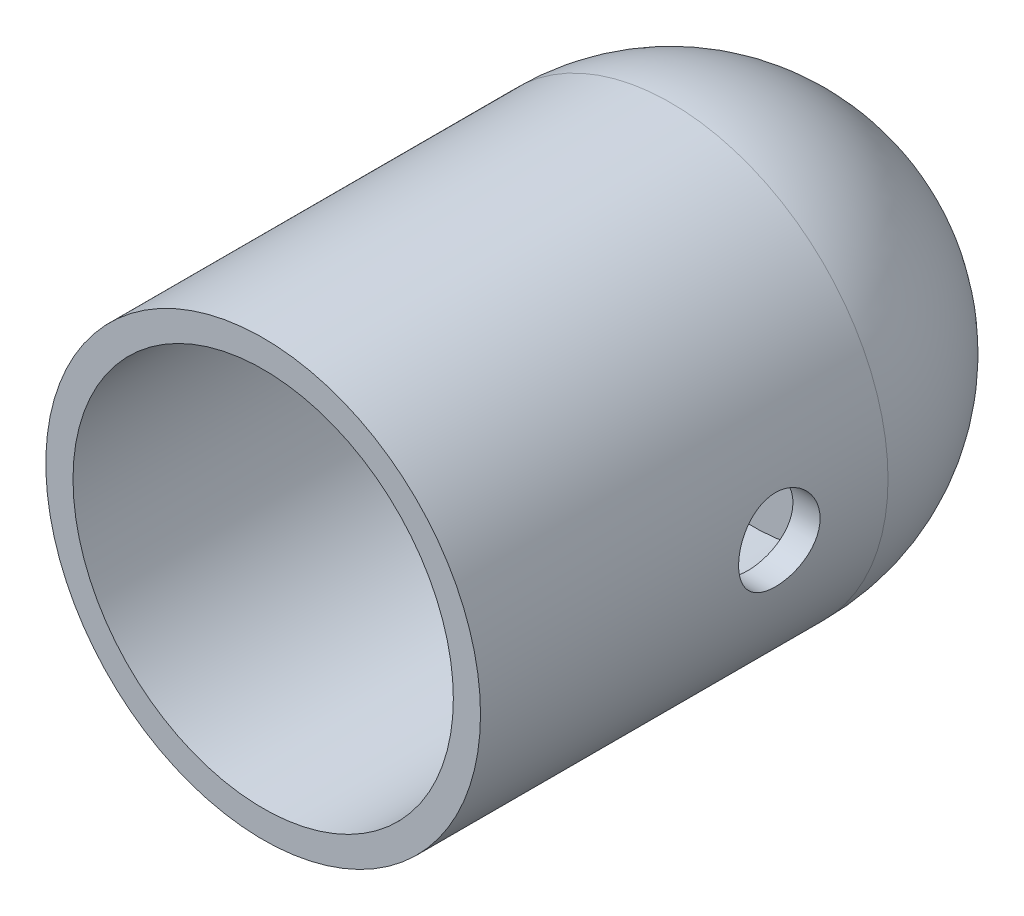
SolidWorks part; units mm, degrees
ref_plane "Front Plane" through (0, 0, 0) normal (0, 0, 1) x (1, 0, 0)
ref_plane "Top Plane" through (0, 0, 0) normal (0, 1, 0) x (1, 0, 0)
ref_plane "Right Plane" through (0, 0, 0) normal (1, 0, 0) x (0, 0, -1)
sketch "Sketch1" plane through (0, 0, 0) normal (0, 0, 1) x (1, 0, 0)
  circle A0 centre (0, 0) radius 40
  dimension "D1" = 80
extrude "Boss-Extrude1" add sketch "Sketch1" along normal mid plane 75
sketch "Sketch3" plane through (0, 0, 0) normal (1, 0, 0) x (0, 0, -1)
  line L1 (-37.5, -40) -> (37.5, -40) construction
  line L2 (37.5, -40) -> (37.5, 40) construction
  circle A0 centre (17.5, 0) radius 7.5
  dimension "D1" = 15
  dimension "D2" = 20
  dimension "D3" = 40
extrude "Cut-Extrude2" cut sketch "Sketch3" against normal through all and the other way through all
sketch "Sketch7" plane through (0, 0, -37.5) normal (0, 0, -1) x (-1, 0, 0)
  line L0 (0, 40) -> (0, -40) construction
  line L1 (0, 40) -> (0, -40)
  arc A0 (0, 40) -> (0, -40) centre (0, 0) ccw
  dimension "D1" = 80
revolve "Revolve1" add sketch "Sketch7" angle 180 about L0
sketch "Sketch2" plane through (0, 0, 37.5) normal (0, 0, 1) x (1, 0, 0)
  circle A0 centre (0, 0) radius 35
  dimension "D1" = 70
extrude "Cut-Extrude3" cut sketch "Sketch2" against normal blind 90
